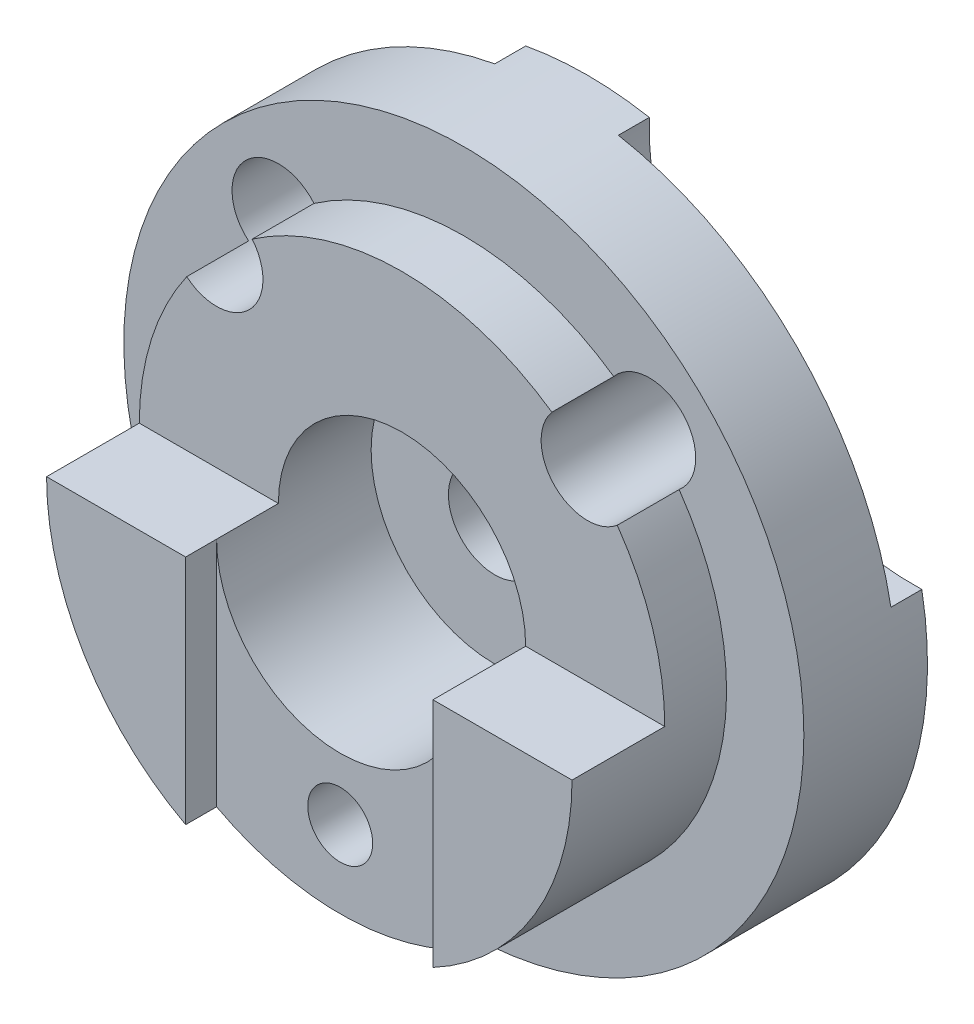
SolidWorks part; units mm, degrees
ref_plane "Front Plane" through (0, 0, 0) normal (0, 0, 1) x (1, 0, 0)
ref_plane "Top Plane" through (0, 0, 0) normal (0, 1, 0) x (1, 0, 0)
ref_plane "Right Plane" through (0, 0, 0) normal (1, 0, 0) x (0, 0, -1)
sketch "Sketch1" plane through (0, 0, 0) normal (0, 0, 1) x (1, 0, 0)
  arc A0 (-55, 0) -> (55, 0) centre (0, 0) ccw
  arc A1 (-55, 0) -> (-10, 45) centre (-55, 45) ccw
  arc A2 (10, 45) -> (55, 0) centre (55, 45) ccw
  arc A3 (-10, 45) -> (10, 45) centre (0, -9.0833) cw
  dimension "D1" = 55
  dimension "D2" = 45
  dimension "D3" = 45
  dimension "D4" = 55
  dimension "D5" = 110
extrude "Boss-Extrude1" add sketch "Sketch1" along normal blind 15
sketch "Sketch2" plane through (0, 0, 15) normal (0, 0, 1) x (1, 0, 0)
  circle A0 centre (0, 0) radius 42.5
  dimension "D1" = 85
extrude "Boss-Extrude2" add sketch "Sketch2" along normal blind 10
sketch "Sketch3" plane through (0, 0, 25) normal (0, 0, 1) x (1, 0, 0)
  arc A0 (-36.2805, 22.1354) -> (-22.2609, 36.2037) centre (-30.104, 30) ccw
  circle A1 centre (0, 0) radius 42.5 construction
  arc A2 (22.2609, 36.2037) -> (36.2805, 22.1354) centre (30.104, 30) ccw
  arc A3 (-22.2609, 36.2037) -> (-36.2805, 22.1354) centre (0, 0) ccw
  arc A4 (22.2609, 36.2037) -> (36.2805, 22.1354) centre (0, 0) cw
  dimension "D1" = 10
  dimension "D3" = 10
  dimension "D4" = 42.5
  dimension "D5" = 42.5
  dimension "D2" = 30
extrude "Cut-Extrude1" cut sketch "Sketch3" against normal blind 10
sketch "Sketch4" plane through (0, 0, 25) normal (0, 0, 1) x (1, 0, 0)
  circle A0 centre (0, 0) radius 55
extrude "Boss-Extrude3" add sketch "Sketch4" along normal blind 15
sketch "Sketch5" plane through (0, 0, 40) normal (0, 0, 1) x (1, 0, 0)
  circle A0 centre (0, 0) radius 42.5
  dimension "D1" = 85
extrude "Cut-Extrude16" cut sketch "Sketch5" against normal blind 5
sketch "Sketch10" plane through (0, 0, 35) normal (0, 0, 1) x (1, 0, 0)
  line L0 (-20, -37.5) -> (-20, 0)
  line L1 (-20, 0) -> (-42.5, 0)
  line L2 (42.5, 0) -> (20, 0)
  line L3 (20, 0) -> (20, -37.5)
  circle A0 centre (0, 0) radius 42.5 construction
  arc A1 (-42.5, 0) -> (-20, -37.5) centre (0, 0) ccw
  circle A2 centre (0, 0) radius 42.5 construction
  arc A3 (20, -37.5) -> (42.5, 0) centre (0, 0) ccw
  dimension "D1" = 22.5
  dimension "D3" = 42.5
  dimension "D2" = 22.5
extrude "Boss-Extrude4" add sketch "Sketch10" along normal blind 10
sketch "Sketch11" plane through (0, 0, 35) normal (0, 0, 1) x (1, 0, 0)
  circle A0 centre (0, 0) radius 20
  circle A1 centre (0, 0) radius 7.5
  dimension "D1" = 15
extrude "Cut-Extrude18" cut sketch "Sketch11" against normal blind 20
sketch "Sketch13" plane through (0, 0, 40) normal (0, 0, 1) x (1, 0, 0)
  line L0 (20, 0) -> (20, -37.5) construction
  circle A0 centre (0, -50) radius 2.5
  dimension "D1" = 5
  dimension "D2" = 50
  dimension "D3" = 20
extrude "Cut-Extrude19" cut sketch "Sketch13" against normal blind 15
sketch "Sketch14" plane through (0, 0, 35) normal (0, 0, 1) x (1, 0, 0)
  circle A0 centre (-30, 30.104) radius 7.5
  arc A1 (42.5, 0) -> (-42.5, 0) centre (0, 0) ccw construction
  circle A2 centre (30, 30.104) radius 7.5
  dimension "D1" = 30
  dimension "D2" = 15
  dimension "D3" = 30
  dimension "15" = 15
extrude "Cut-Extrude20" cut sketch "Sketch14" against normal blind 20
sketch "Sketch16" plane through (0, 0, 40) normal (0, 0, 1) x (1, 0, 0)
  circle A0 centre (-30, 30.104) radius 7.5
  circle A2 centre (30, 30.104) radius 7.5
  circle A3 centre (0, 0) radius 42.5 construction
  arc A4 (-34.8246, 24.3618) -> (-24.2411, 34.9087) centre (0, 0) cw
  arc A5 (24.2411, 34.9087) -> (34.8246, 24.3618) centre (0, 0) cw
  point P0 (-30, 30.104)
  point P1 (30, 30.104)
  arc M3 (-42.5, 0) -> (42.5, 0) centre (0, 0) cw
  dimension "D1" = 15
  dimension "D2" = 15
  dimension "D3" = 42.5
  dimension "D4" = 42.5
extrude "Cut-Extrude21" cut sketch "Sketch16" against normal blind 20 contours A0 M3 | A2 M3
sketch "Sketch23" plane through (0, 0, 15) normal (0, 0, -1) x (-1, 0, 0)
  circle A0 centre (0, 0) radius 55
extrude "Boss-Extrude5" add sketch "Sketch23" along normal blind 10
sketch "Sketch24" plane through (0, 0, 15) normal (0, 0, 1) x (1, 0, 0)
  circle A1 centre (0, 0) radius 55
  circle A2 centre (0, 0) radius 55
  dimension "D1" = 0
extrude "Boss-Extrude6" add sketch "Sketch24" along normal blind 10
sketch "Sketch25" plane through (0, 0, 0) normal (1, 0, 0) x (0, 0, -1)
  line L0 (-5, 55) -> (-40, 55) construction
  line L1 (-45, 0) -> (-30, 0)
  line L2 (-45, 0) -> (-45, 55)
  line L3 (-45, 55) -> (-30, 55)
  line L4 (-30, 0) -> (-30, 55)
  dimension "D1" = 15
extrude "Cut-Extrude22" cut sketch "Sketch25" against normal mid plane 140
sketch "Sketch26" plane through (0, 0, 25) normal (0, 0, 1) x (1, 0, 0)
  circle A0 centre (30, 30.104) radius 7.5 construction
  circle A1 centre (-30, 30.104) radius 7.5 construction
  circle A2 centre (30, 30.104) radius 7.5
  circle A3 centre (-30, 30.104) radius 7.5
extrude "Cut-Extrude23" cut sketch "Sketch26" against normal blind 140
sketch "Sketch27" plane through (0, 0, 35) normal (0, 0, 1) x (1, 0, 0)
  line L1 (7.5, 0) -> (-7.5, 0)
  line L3 (-7.5, 0) -> (7.5, 0)
  line L4 (-7.5, 0) -> (7.5, 0)
  line L6 (7.5, 0) -> (-7.5, 0)
  arc A1 (-7.5, 0) -> (7.5, 0) centre (0, 0) ccw
  arc A2 (-7.5, 0) -> (7.5, 0) centre (0, 0) ccw
  arc A3 (7.5, 0) -> (-7.5, 0) centre (0, 0) ccw
  arc A4 (7.5, 0) -> (-7.5, 0) centre (0, 0) ccw
  line M5 (7.5, 0) -> (-7.5, 0)
  arc M6 (-7.5, 0) -> (7.5, 0) centre (0, 0) ccw
  dimension "D1" = 0
  dimension "D2" = 0
extrude "Cut-Extrude24" cut sketch "Sketch27" against normal blind 140 contours M6 M5 | A4 M5
sketch "Sketch29" plane through (0, 0, 25) normal (0, 0, 1) x (1, 0, 0)
  circle A1 centre (0, 0) radius 20
  circle A7 centre (0, 0) radius 20
  dimension "D1" = 0
extrude "Cut-Extrude25" cut sketch "Sketch29" against normal blind 10
sketch "Sketch33" plane through (0, 0, 30) normal (0, 0, 1) x (1, 0, 0)
  line L0 (-61.5732, 0) -> (61.5732, 0)
  arc A0 (42.5, 0) -> (-42.5, 0) centre (0, 0) ccw
  arc A1 (61.5732, 0) -> (-61.5732, 0) centre (0, 0) ccw
  circle M1 centre (30, 30.104) radius 7.5
  circle M2 centre (-30, 30.104) radius 7.5
  arc M4 (55, 0) -> (-55, 0) centre (0, 0) ccw
  line M5 (-55, 0) -> (-20, 0)
extrude "Cut-Extrude28" cut sketch "Sketch33" against normal blind 10 contours A0 L0 M4 M5 M2 M1
sketch "Sketch34" plane through (0, 0, 5) normal (0, 0, -1) x (-1, 0, 0)
  line L0 (0, 0) -> (0, 19.5231)
  arc A0 (-54.0833, 10) -> (-10, 54.0833) centre (-52.7294, 52.7294) ccw
  arc A1 (54.0833, 10) -> (10, 54.0833) centre (52.7294, 52.7294) cw
  arc A4 (10, 45) -> (55, 0) centre (55, 45) ccw
  arc A5 (55, 0) -> (-55, 0) centre (0, 0) ccw
  arc A6 (-55, 0) -> (-10, 45) centre (-55, 45) ccw
  arc A7 (10, 45) -> (-10, 45) centre (0, -9.0833) ccw
  arc A8 (10, 45) -> (55, 0) centre (55, 45) ccw
  arc A9 (55, 0) -> (-55, 0) centre (0, 0) ccw
  arc A10 (-55, 0) -> (-10, 45) centre (-55, 45) ccw
  arc A11 (10, 45) -> (-10, 45) centre (0, -9.0833) ccw
  point P6 (-22.5, 22.5)
  arc M8 (10, 45) -> (55, 0) centre (55, 45) ccw
  arc M9 (55, 0) -> (-55, 0) centre (0, 0) ccw
  arc M10 (-55, 0) -> (-10, 45) centre (-55, 45) ccw
  arc M11 (-10, 45) -> (10, 45) centre (0, -9.0833) cw
  dimension "D2" = 10
  dimension "D3" = 10
  dimension "D4" = 22.5
  dimension "D1" = 0
extrude "Boss-Extrude8" add sketch "Sketch34" along normal blind 5 contours A1 A0 M9 M10 M11 M8
sketch "Sketch35" plane through (0, 0, 35) normal (0, 0, 1) x (1, 0, 0)
  point P0 (0, -30)
  dimension "D1" = 30
hole_wizard "M12x1.5 Tapped Hole1" positions "3DSketch1" profile "Sketch36" tap size "M12x1.5" standard "ISO"
sketch3d "3DSketch1"
  point P0 (0, -30, 35)
sketch "Sketch36" plane through (0, -30, 35) normal (1, 0, 0) x (0, -1, 0)
  line L0 (0, 0) -> (0, 13.1545)
  line L1 (0, 13.1545) -> (5.25, 10)
  line L2 (5.25, 10) -> (5.25, 0)
  line L5 (5.25, 0) -> (0, 0)
  line L10 (0, 13.1545) -> (-5.25, 10) construction
  line L11 (0, -6.35) -> (0, 107.95) construction
  dimension "Tap Drill Dia." = 10.5
  dimension "Tap Drill Depth" = 10
  dimension "Drill Angle" = 118
sketch "Sketch37" plane through (0, 0, 0) normal (0, 1, 0) x (1, 0, 0)
  line L1 (-55, -20) -> (-42.5, -20)
  line L2 (-55, -20) -> (-55, -45)
  line L3 (-55, -45) -> (-42.5, -45)
  line L4 (-42.5, -20) -> (-42.5, -45)
  line L5 (55, -20) -> (42.5, -20)
  line L6 (55, -20) -> (55, -45)
  line L7 (55, -45) -> (42.5, -45)
  line L8 (42.5, -20) -> (42.5, -45)
extrude "Cut-Extrude29" cut sketch "Sketch37" against normal blind 75
sketch "Sketch38" plane through (0, 0, 40) normal (0, 0, 1) x (1, 0, 0)
  line L10 (-42.5, 0) -> (-42.5, -34.9106)
  line L11 (-42.5, 0) -> (-42.5, -34.9106)
  line L14 (42.5, -34.9106) -> (42.5, 0)
  line L15 (42.5, -34.9106) -> (42.5, 0)
  arc A12 (20, -37.5) -> (42.5, 0) centre (0, 0) ccw
  arc A13 (20, -37.5) -> (42.5, 0) centre (0, 0) ccw
  arc A14 (-42.5, -34.9106) -> (42.5, -34.9106) centre (0, 0) ccw
  arc A19 (-20, -37.5) -> (20, -37.5) centre (0, 0) ccw
  arc A20 (-42.5, -34.9106) -> (42.5, -34.9106) centre (0, 0) ccw
  arc A24 (-20, -37.5) -> (20, -37.5) centre (0, 0) ccw
  arc A25 (-42.5, 0) -> (-20, -37.5) centre (0, 0) ccw
  arc A26 (-42.5, 0) -> (-20, -37.5) centre (0, 0) ccw
  dimension "D1" = 0
extrude "Cut-Extrude30" cut sketch "Sketch38" against normal blind 20
sketch "Sketch39" plane through (0, 0, 20) normal (0, 0, 1) x (1, 0, 0)
  circle A0 centre (0, -50) radius 2.5
  dimension "D2" = 5
  dimension "D1" = 50
extrude "Cut-Extrude31" cut sketch "Sketch39" against normal blind 20
sketch "Sketch41" plane through (0, 0, 35) normal (0, 0, 1) x (1, 0, 0)
  line L2 (-20, 0) -> (-20, -37.5)
  line L3 (20, -37.5) -> (20, 0)
  line L4 (-20, 0) -> (-20, -37.5)
  line L5 (20, -37.5) -> (20, 0)
  circle A0 centre (0, -30) radius 5.25 construction
  circle A1 centre (0, -30) radius 5.25
  arc A2 (-20, 0) -> (20, 0) centre (0, 0) ccw
  arc A3 (-20, -37.5) -> (20, -37.5) centre (0, 0) ccw
  arc A4 (-20, 0) -> (20, 0) centre (0, 0) ccw
  arc A5 (-20, -37.5) -> (20, -37.5) centre (0, 0) ccw
  dimension "D1" = 0
extrude "Boss-Extrude17" add sketch "Sketch41" along normal blind 5
